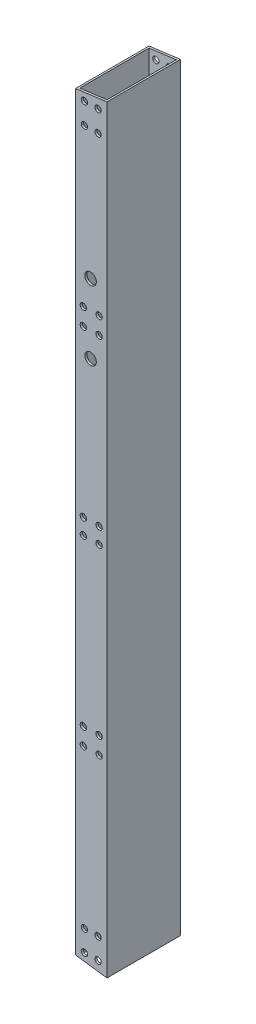
SolidWorks part; units mm, degrees
ref_plane "前视基准面" through (0, 0, 0) normal (0, 0, 1) x (1, 0, 0)
ref_plane "上视基准面" through (0, 0, 0) normal (0, 1, 0) x (1, 0, 0)
ref_plane "右视基准面" through (0, 0, 0) normal (1, 0, 0) x (0, 0, -1)
other "Configuration Table"
sketch "草图1" plane through (0, 0, 0) normal (0, 0, 1) x (1, 0, 0)
  line L1 (15, -375) -> (-15, -375)
  line L2 (15, -375) -> (15, 375)
  line L3 (15, 375) -> (-15, 375)
  line L4 (-15, -375) -> (-15, 375)
  line L5 (15, -375) -> (-15, 375) construction
  line L6 (15, 375) -> (-15, -375) construction
  circle A0 centre (-7.5, 194.9781) radius 2
  circle A1 centre (7.5, 194.9781) radius 2
  circle A2 centre (-7.5, 178.7736) radius 2
  circle A3 centre (7.5, 178.7736) radius 2
  circle A4 centre (-7.5, -150.8775) radius 2
  circle A5 centre (7.5, -150.8775) radius 2
  circle A6 centre (-7.5, -167.082) radius 2
  circle A7 centre (7.5, -167.082) radius 2
  point P0 (0, 0)
  dimension "D1" = 30
  dimension "D2" = 750
extrude "凸台-拉伸2" add sketch "草图1" along normal blind 70
sketch "草图2" plane through (0, -375, 0) normal (0, -1, 0) x (1, 0, 0)
  line L0 (-15, 70) -> (-15, 0) construction
  line L1 (-13, 68) -> (13, 68)
  line L2 (-13, 68) -> (-13, 2)
  line L3 (-13, 2) -> (13, 2)
  line L4 (13, 68) -> (13, 2)
  line L5 (-13, 68) -> (13, 2) construction
  line L6 (-13, 2) -> (13, 68) construction
  line L7 (-15, 70) -> (15, 70) construction
  line L8 (15, 70) -> (15, 0) construction
  line L9 (-15, 0) -> (15, 0) construction
  point P0 (0, 35)
  dimension "D1" = 2
  dimension "D2" = 2
  dimension "D3" = 2
  dimension "D4" = 2
extrude "切除-拉伸3" cut sketch "草图2" against normal through all contours L2 L1 L4 L3
sketch "草图3" plane through (0, 0, 70) normal (0, 0, 1) x (1, 0, 0)
  line L0 (15, 375) -> (-15, 371.0504)
  line L1 (-15, 375) -> (-15, -375) construction
  line L2 (15, -375) -> (15, 375) construction
  line L3 (15, -347.1) -> (-15, -343.1504)
  line L4 (-15, -343.1504) -> (-15, -376.6872)
  line L5 (-15, -376.6872) -> (15, -376.6872)
  line L6 (15, -376.6872) -> (15, -347.1)
  line L7 (-15, 371.0504) -> (-15, 377.0408)
  line L8 (-15, 377.0408) -> (15, 377.0408)
  line L9 (15, 377.0408) -> (15, 375)
  line M2 (-15, 375) -> (-15, -375)
  line M3 (-15, -375) -> (15, -375)
  line M4 (15, -375) -> (15, 375)
  dimension "D1" = 82.5
  dimension "D2" = 82.5
  dimension "D3" = 722.1
extrude "切除-拉伸4" cut sketch "草图3" against normal through all contours L3 M4 M2 M3 | L9 L0 L7 L8
sketch "草图8" plane through (0, 0, 0) normal (0, 0, -1) x (-1, 0, 0)
  line L5 (15, 371.0504) -> (15, -343.1504) construction
  line L6 (15, 371.0504) -> (15, -343.1504)
  line L7 (-15, -347.1) -> (-15, 375) construction
  line L8 (-15, -347.1) -> (-15, 375)
  line L12 (-15, 13.95) -> (15, 13.95)
  circle A13 centre (6.5, 364.8704) radius 3
  circle A14 centre (-6.5, 364.8704) radius 3
  circle A15 centre (-6.5, 344.8704) radius 3
  circle A16 centre (6.5, 344.8704) radius 3
  circle A17 centre (-7.5, -150.8775) radius 3
  circle A18 centre (7.5, -150.8775) radius 3
  circle A19 centre (7.5, -167.082) radius 3
  circle A20 centre (-7.5, -167.082) radius 3
  circle A21 centre (-7.5, 21.448) radius 3
  circle A22 centre (7.5, 21.448) radius 3
  circle A23 centre (-7.5, 6.448) radius 3
  circle A24 centre (7.5, 6.448) radius 3
  circle A25 centre (-7.5, 194.9781) radius 3
  circle A26 centre (-7.5, 178.7736) radius 3
  circle A27 centre (7.5, 194.9781) radius 3
  circle A28 centre (7.5, 178.7736) radius 3
  circle A29 centre (6.5, -316.9704) radius 3
  circle A30 centre (-6.5, -316.9704) radius 3
  circle A31 centre (-6.5, -336.9704) radius 3
  circle A32 centre (6.5, -336.9704) radius 3
  point P67 (0, 0)
  point P68 (0, 0)
  dimension "D5" = 6
  dimension "D6" = 6
  dimension "D7" = 6
  dimension "D8" = 6
  dimension "D9" = 6
  dimension "D10" = 6
  dimension "D11" = 6
  dimension "D12" = 6
  dimension "D13" = 6
  dimension "D14" = 6
  dimension "D15" = 6
  dimension "D16" = 6
  dimension "D17" = 6
  dimension "D18" = 6
  dimension "D19" = 6
  dimension "D20" = 6
extrude "切除-拉伸6" cut sketch "草图8" against normal through all
sketch "草图9" plane through (0, 0, 70) normal (0, 0, 1) x (1, 0, 0)
  circle A0 centre (-0.6127, 155.5023) radius 5.5
  circle A1 centre (-0.6127, 221.5023) radius 5.5
  dimension "D1" = 11
  dimension "D2" = 11
extrude "切除-拉伸7" cut sketch "草图9" against normal blind 316
